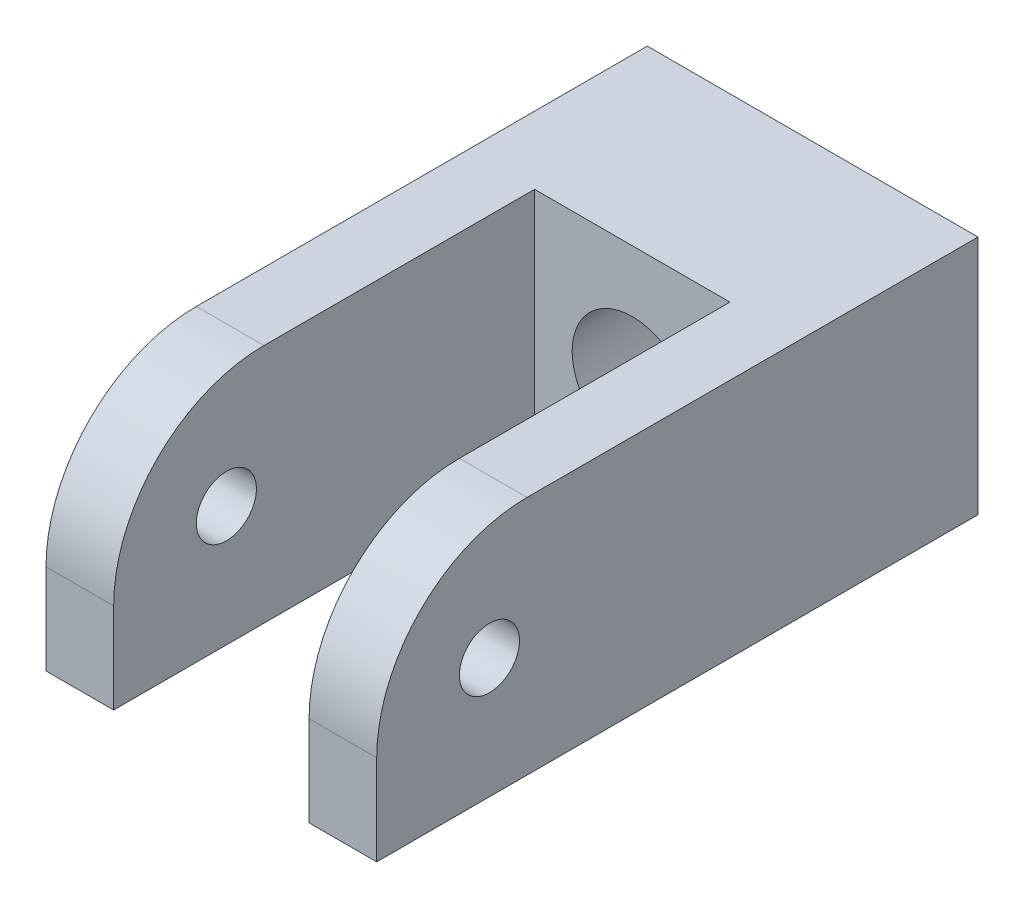
SolidWorks part; units mm, degrees
ref_plane "Front Plane" through (0, 0, 0) normal (0, 0, 1) x (1, 0, 0)
ref_plane "Top Plane" through (0, 0, 0) normal (0, 1, 0) x (1, 0, 0)
ref_plane "Right Plane" through (0, 0, 0) normal (1, 0, 0) x (0, 0, -1)
sketch "Sketch1" plane through (0, 0, 0) normal (0, 1, 0) x (1, 0, 0)
  line L0 (-11, 20) -> (-11, -20)
  line L1 (-11, -20) -> (-6.5, -20)
  line L2 (-6.5, -20) -> (-6.5, 8)
  line L3 (-6.5, 8) -> (6.5, 8)
  line L4 (6.5, 8) -> (6.5, -20)
  line L5 (6.5, -20) -> (11, -20)
  line L6 (11, -20) -> (11, 20)
  line L7 (11, 20) -> (-11, 20)
  line L8 (-11, -20) -> (11, 20) construction
  dimension "D1" = 28
  dimension "D2" = 13
  dimension "D3" = 40
  dimension "D4" = 4.5
extrude "Boss-Extrude1" add sketch "Sketch1" along normal blind 16
fillet "Fillet1" radius 10 2 edges at (-8.75, 16, 20) (8.75, 16, 20)
sketch "Sketch2" plane through (0, 0, -20) normal (0, 0, -1) x (-1, 0, 0)
  circle A0 centre (0, 7.9209) radius 4
  dimension "D1" = 8
extrude "Cut-Extrude1" cut sketch "Sketch2" against normal blind 16
sketch "Sketch3" plane through (-11, 0, 0) normal (-1, 0, 0) x (0, 0, 1)
  circle A0 centre (12.5, 8) radius 2
  dimension "D1" = 4
  dimension "D2" = 12.5
  dimension "D3" = 8
extrude "Cut-Extrude2" cut sketch "Sketch3" against normal blind 24
